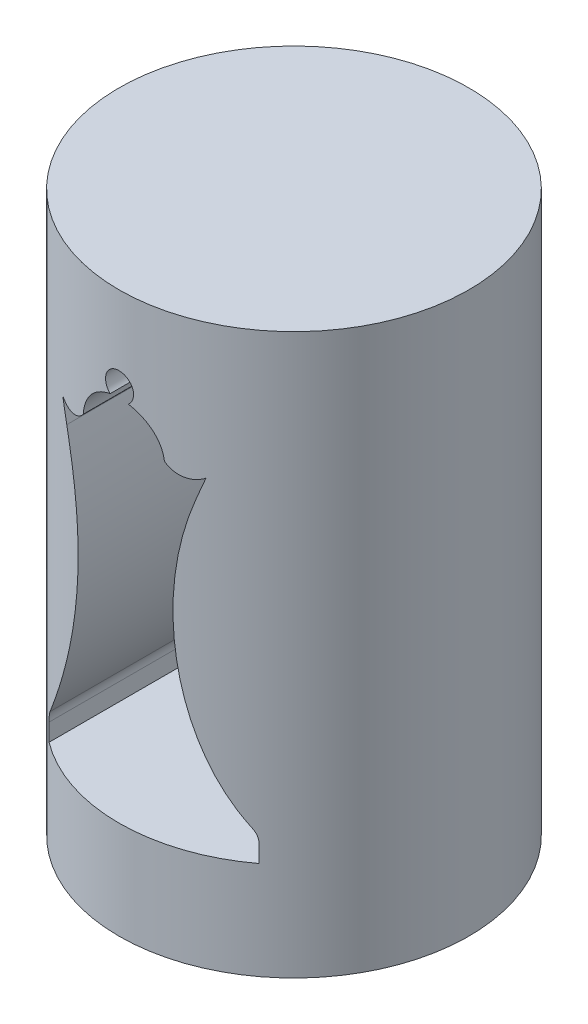
SolidWorks part; units mm, degrees
ref_plane "Front" through (0, 0, 0) normal (0, 0, 1) x (1, 0, 0)
ref_plane "Top" through (0, 0, 0) normal (0, 1, 0) x (1, 0, 0)
ref_plane "Right" through (0, 0, 0) normal (1, 0, 0) x (0, 0, -1)
sketch "Sketch2" plane through (0, 0, 0) normal (0, 1, 0) x (1, 0, 0)
  circle A0 centre (0, 0) radius 12.5
  dimension "D1" = 25
extrude "Boss-Extrude1" add sketch "Sketch2" along normal mid plane 40
sketch "Sketch3" plane through (0, 0, 0) normal (0, 0, 1) x (1, 0, 0)
  line L0 (-7.5, -13) -> (7.5, -13)
  line L2 (-7.5, -11.75) -> (-7.5, -13)
  line L18 (-4.6158, 8.9091) -> (-5.1189, 10.3579)
  line L19 (0, -50) -> (0, 50) construction
  line L20 (4.6158, 8.9091) -> (5.1189, 10.3579)
  line L21 (7.5, -11.75) -> (7.5, -13)
  arc A4 (-7.2252, -10.8563) -> (-7.5, -11.75) centre (-5.9096, -11.75) ccw
  arc A30 (-7.2252, -10.8563) -> (-4.6158, 8.9091) centre (-25.5963, 1.6239) ccw
  arc A31 (5.1189, 10.3579) -> (2.8998, 10.6813) centre (4.1829, 11.71) cw
  arc A32 (-5.1189, 10.3579) -> (-2.8998, 10.6813) centre (-4.1829, 11.71) ccw
  arc A34 (7.2252, -10.8563) -> (4.6158, 8.9091) centre (25.5963, 1.6239) cw
  arc A35 (7.2252, -10.8563) -> (7.5, -11.75) centre (5.9096, -11.75) cw
  arc A36 (-2.8998, 10.6813) -> (-0.6513, 13.2412) centre (0, 10.4017) cw
  arc A37 (0.6513, 13.2412) -> (-0.6513, 13.2412) centre (0, 14) ccw
  arc A38 (0.6513, 13.2412) -> (2.8998, 10.6813) centre (0, 10.4017) cw
  point P0 (0, -13)
  dimension "D1" = 27
  dimension "D6" = 1.25
  dimension "D4" = 1
  dimension "D2" = 15
  dimension "D3" = 13
extrude "Cut-Extrude1" cut sketch "Sketch3" against normal through all both and the other way through all
sketch "Sketch4" plane through (0, -20, 0) normal (0, -1, 0) x (-1, 0, 0)
  circle A0 centre (0, 0) radius 3
  dimension "D1" = 6
extrude "Cut-Extrude2" cut sketch "Sketch4" against normal blind 3
